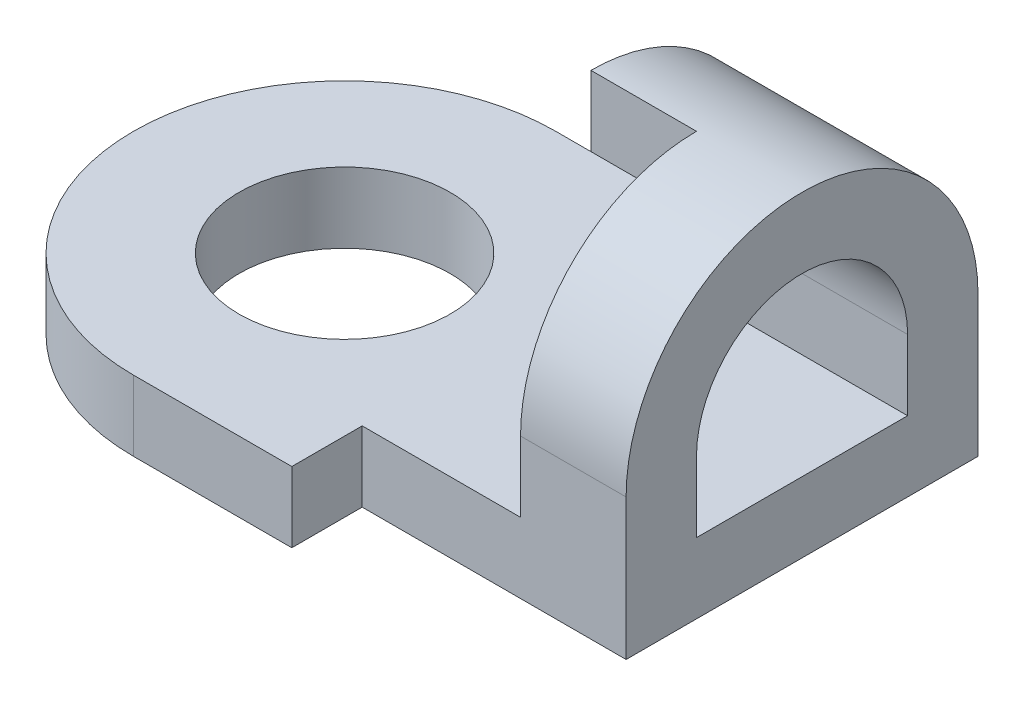
SolidWorks part; units mm, degrees
ref_plane "Front" through (0, 0, 0) normal (0, 0, 1) x (1, 0, 0)
ref_plane "Top" through (0, 0, 0) normal (0, 1, 0) x (1, 0, 0)
ref_plane "Right" through (0, 0, 0) normal (1, 0, 0) x (0, 0, -1)
sketch "Sketch1" plane through (0, 0, 0) normal (0, 1, 0) x (1, 0, 0)
  line L1 (-6, -6) -> (6, -6)
  line L2 (-6, -6) -> (-6, 6)
  line L3 (-6, 6) -> (6, 6)
  line L4 (6, -6) -> (6, 6)
  line L5 (-6, -6) -> (6, 6) construction
  line L6 (-6, 6) -> (6, -6) construction
  line L7 (6, -6) -> (-1.5, -6)
  line L8 (6, -6) -> (6, -4)
  line L9 (6, -4) -> (-1.5, -4)
  line L10 (-1.5, -6) -> (-1.5, -4)
  arc A0 (-6, 6) -> (-6, -6) centre (-6, 0) ccw
  circle A1 centre (-6, 0) radius 3
  point P0 (0, 0)
  dimension "D3" = 6
  dimension "D1" = 12
  dimension "D2" = 12
  dimension "D4" = 2
  dimension "D5" = 7.5
extrude "Boss-Extrude1" add sketch "Sketch1" along normal blind 2 contours A1 L2 A0 | A1 L2 L1 L4 L3
sketch "Sketch2" plane through (6, 0, 0) normal (1, 0, 0) x (0, 0, -1)
  line L0 (4, 2) -> (4, 4)
  line L1 (-2, 4) -> (-2, 2)
  line L2 (-2, 2) -> (-4, 2)
  line L3 (-4, 2) -> (-4, 4)
  line L4 (6, 4) -> (6, 2)
  line L5 (6, 2) -> (4, 2)
  line L6 (6, 2) -> (-6, 2) construction
  arc A0 (4, 4) -> (-2, 4) centre (1, 4) ccw
  arc A1 (-4, 4) -> (6, 4) centre (1, 4) cw
  point P2 (0, 0)
  point P12 (5.8495, 2.1932)
  point P14 (0, 0)
  point P16 (4.7011, 2)
  point P19 (-2.7399, 2)
  point P20 (-2, 6.1675)
  dimension "D1" = 2
  dimension "D2" = 2
  dimension "D3" = 2
extrude "Boss-Extrude2" add sketch "Sketch2" against normal blind 6
sketch "Sketch3" plane through (0, 0, 0) normal (-1, 0, 0) x (0, 0, 1)
  line L1 (-1, 9) -> (4, 9)
  line L2 (-1, 9) -> (-1, 2)
  line L3 (-1, 2) -> (4, 2)
  line L4 (4, 9) -> (4, 2)
  arc A0 (4, 4) -> (-6, 4) centre (-1, 4) ccw construction
extrude "Cut-Extrude1" cut sketch "Sketch3" against normal blind 3
